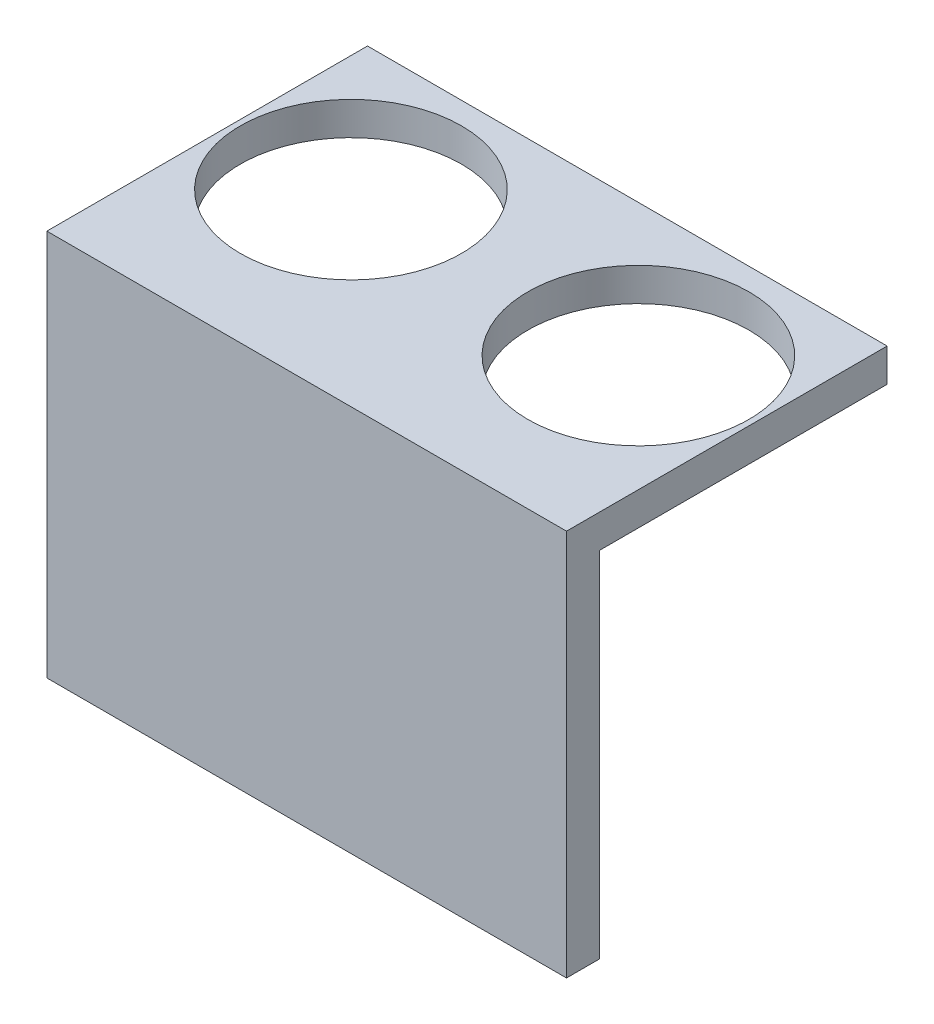
SolidWorks part; units mm, degrees
ref_plane "Front Plane" through (0, 0, 0) normal (0, 0, 1) x (1, 0, 0)
ref_plane "Top Plane" through (0, 0, 0) normal (0, 1, 0) x (1, 0, 0)
ref_plane "Right Plane" through (0, 0, 0) normal (1, 0, 0) x (0, 0, -1)
sketch "Sketch1" plane through (0, 0, 0) normal (0, 1, 0) x (1, 0, 0)
  line L0 (0, 12) -> (0, -12)
  line L1 (-23.5, -12) -> (23.5, -12)
  line L2 (-23.5, -12) -> (-23.5, 12)
  line L3 (-23.5, 12) -> (23.5, 12)
  line L4 (23.5, -12) -> (23.5, 12)
  line L8 (23, 0) -> (23.5, 0)
  circle A0 centre (-13, 0) radius 10
  circle A1 centre (13, 0) radius 10
  point P0 (0, 0)
  point P9 (0, 0)
  point P16 (0, 0)
  dimension "D3" = 20
  dimension "D4" = 20
  dimension "D1" = 47
  dimension "D2" = 24
  dimension "D5" = 24
  dimension "D6" = 13
  dimension "D7" = 13
  dimension "D8" = 12
  dimension "D9" = 12
extrude "Boss-Extrude1" add sketch "Sketch1" along normal blind 3
sketch "Sketch2" plane through (0, 3, 0) normal (0, 1, 0) x (1, 0, 0)
  line L1 (-23.5, -12) -> (23.5, -12)
  line L2 (-23.5, -12) -> (-23.5, -14)
  line L3 (-23.5, -14) -> (23.5, -14)
  line L4 (23.5, -12) -> (23.5, -14)
  dimension "D1" = 2
  dimension "D2" = 47
extrude "Boss-Extrude2" add sketch "Sketch2" against normal blind 3
sketch "Sketch3" plane through (0, 3, 0) normal (0, 1, 0) x (1, 0, 0)
  line L1 (-23.5, -14) -> (23.5, -14)
  line L2 (-23.5, -14) -> (-23.5, -17)
  line L3 (-23.5, -17) -> (23.5, -17)
  line L4 (23.5, -14) -> (23.5, -17)
  dimension "D1" = 47
  dimension "D2" = 3
extrude "Boss-Extrude6" add sketch "Sketch3" against normal blind 35 contours L2 L1 L4 L3
